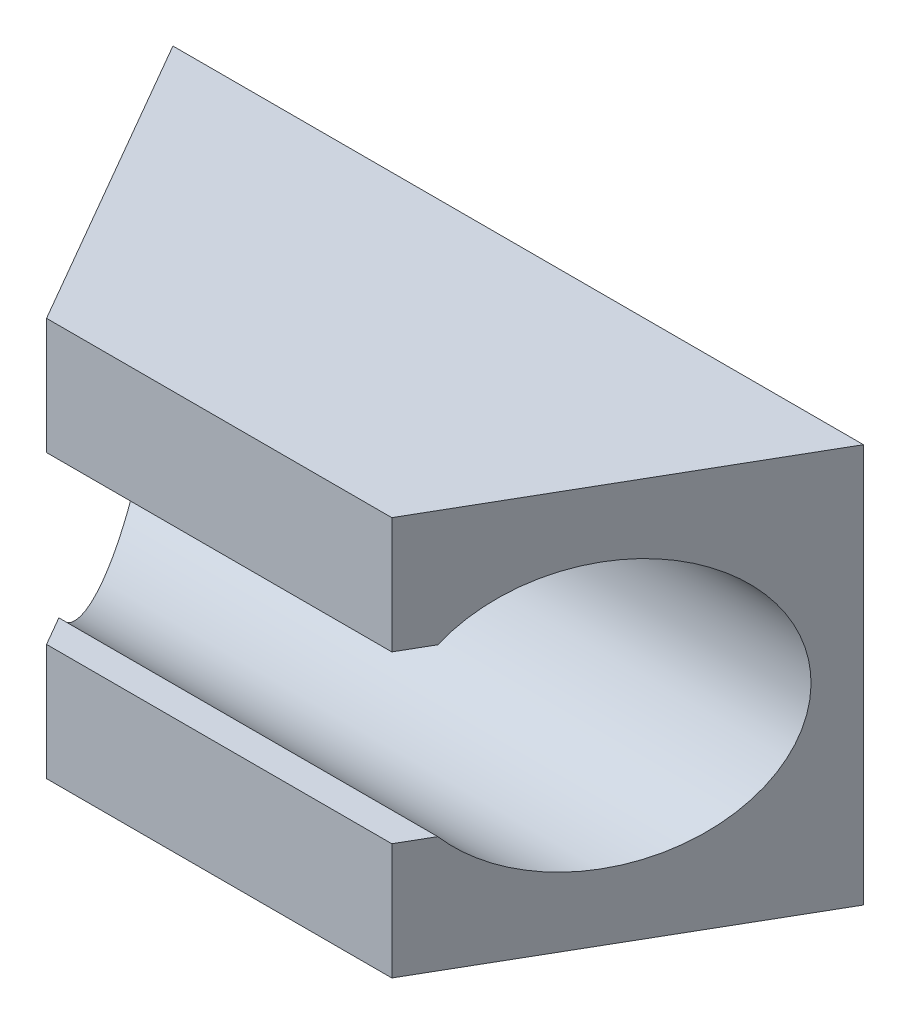
SolidWorks part; units mm, degrees
ref_plane "Front Plane" through (0, 0, 0) normal (0, 0, 1) x (1, 0, 0)
ref_plane "Top Plane" through (0, 0, 0) normal (0, 1, 0) x (1, 0, 0)
ref_plane "Right Plane" through (0, 0, 0) normal (1, 0, 0) x (0, 0, -1)
sketch "Sketch8" plane through (0, 0, 0) normal (0, 0, 1) x (1, 0, 0)
  line L0 (4.1243, 3) -> (-4.1243, 3) construction
  line L1 (5.1962, -3) -> (-5.1962, -3)
  line L2 (5.1962, -3) -> (5.1962, 3)
  line L3 (5.1962, 3) -> (-5.1962, 3)
  line L4 (-5.1962, -3) -> (-5.1962, 3)
  circle A0 centre (0, 0) radius 6 construction
extrude "Boss-Extrude3" add sketch "Sketch8" along normal blind 4.5
sketch "Sketch9" plane through (5.1962, 0, 0) normal (1, 0, 0) x (0, 0, -1)
  line L0 (-0.5, 0) -> (-2.5, 0) construction
  line L1 (0, -3) -> (0, 3) construction
  line L2 (-4.5, -3) -> (-4.5, 3) construction
  line L3 (-4.0612, 1.25) -> (-4.5, 1.25)
  line L4 (-4.0612, 1.25) -> (-4.0612, -1.25) construction
  line L5 (-4.0612, -1.25) -> (-4.5, -1.25)
  line L6 (-4.5, 1.25) -> (-4.5, -1.25)
  arc A0 (-4.0612, -1.25) -> (-4.0612, 1.25) centre (-2.5, 0) ccw
  dimension "D1" = 4
  dimension "D2" = 2.5
  dimension "D3" = 0.5
extrude "Cut-Extrude5" cut sketch "Sketch9" against normal through all
sketch "Sketch10" plane through (0, -3, 0) normal (0, -1, 0) x (1, 0, 0)
  line L0 (5.1962, 0) -> (2.5981, 4.5)
  line L1 (-5.1962, 4.5) -> (5.1962, 4.5) construction
  line L2 (2.5981, 4.5) -> (5.1962, 4.5)
  line L3 (5.1962, 4.5) -> (5.1962, 0)
  line L4 (0, 0) -> (0, 4.5) construction
  line L5 (-5.1962, 4.5) -> (-5.1962, 0)
  line L6 (-2.5981, 4.5) -> (-5.1962, 4.5)
  line L7 (-5.1962, 0) -> (-2.5981, 4.5)
  dimension "D1" = 60
extrude "Cut-Extrude6" cut sketch "Sketch10" against normal through all
